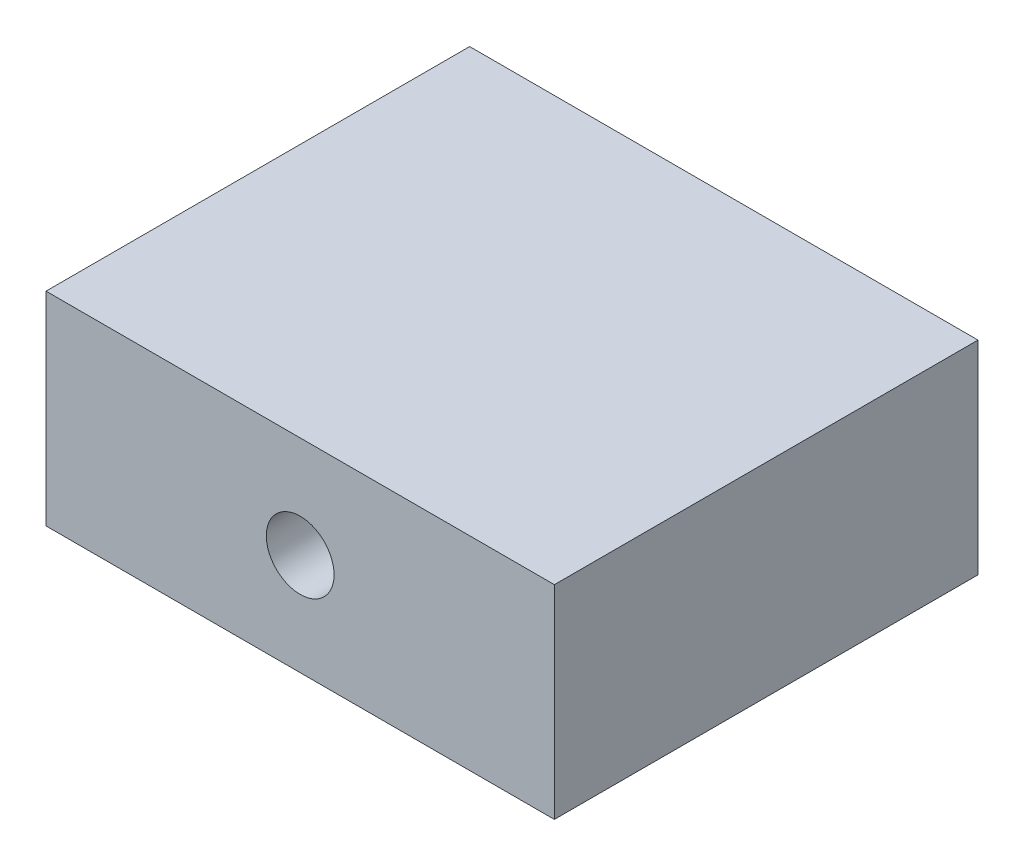
SolidWorks part; units mm, degrees
ref_plane "Front Plane" through (0, 0, 0) normal (0, 0, 1) x (1, 0, 0)
ref_plane "Top Plane" through (0, 0, 0) normal (0, 1, 0) x (1, 0, 0)
ref_plane "Right Plane" through (0, 0, 0) normal (1, 0, 0) x (0, 0, -1)
sketch "草图1" plane through (0, 0, 0) normal (0, 1, 0) x (1, 0, 0)
  line L1 (0, 0) -> (30, 0)
  line L2 (0, 0) -> (0, 25)
  line L3 (0, 25) -> (30, 25)
  line L4 (30, 0) -> (30, 25)
extrude "凸台-拉伸1" add sketch "草图1" along normal blind 12
sketch "草图2" plane through (0, 0, 0) normal (0, 0, 1) x (1, 0, 0)
  line L0 (0, 12) -> (30, 0)
  line L1 (30, 0) -> (30, 12)
  line L2 (30, 12) -> (0, 0)
  circle A0 centre (15, 6) radius 2
extrude "切除-拉伸1" cut sketch "草图2" against normal blind 25 contours L2 A0 L0 | L0 A0 L2 | L2 A0 L0 | L0 A0 L2
sketch "草图3" plane through (0, 0, 0) normal (0, 0, 1) x (1, 0, 0)
  circle A0 centre (15, 6) radius 2
  point P0 (15, 6)
sketch "草图4" plane through (0, 0, -25) normal (0, 0, -1) x (-1, 0, 0)
  circle A0 centre (-15, 6) radius 2
  point P0 (-15, 6)
sketch "草图5" plane through (0, 0, 0) normal (0, -1, 0) x (1, 0, 0)
